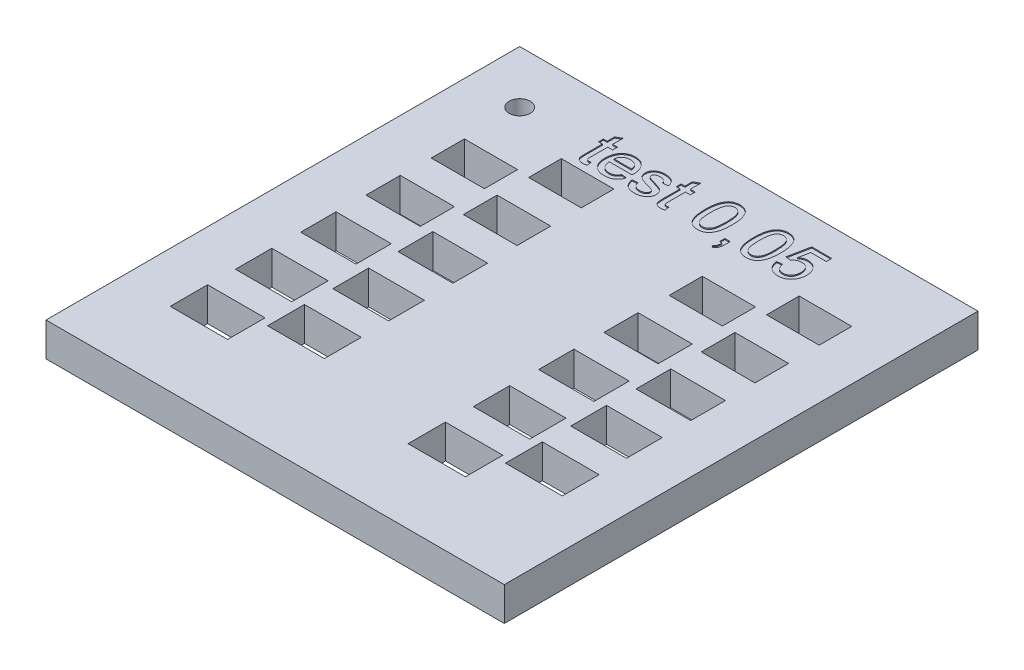
SolidWorks part; units mm, degrees
ref_plane "Спереди" through (0, 0, 0) normal (0, 0, 1) x (1, 0, 0)
ref_plane "Сверху" through (0, 0, 0) normal (0, 1, 0) x (1, 0, 0)
ref_plane "Справа" through (0, 0, 0) normal (1, 0, 0) x (0, 0, -1)
sketch "Эскиз1" plane through (0, 0, 0) normal (0, 1, 0) x (1, 0, 0)
  line L0 (0.0889, -0.0341) -> (43.6285, -0.0341)
  line L1 (43.6285, -0.0341) -> (43.6285, 44.9659)
  line L2 (43.6285, 44.9659) -> (0.0889, 44.9659)
  line L3 (0.0889, 44.9659) -> (0.0889, -0.0341)
  line L5 (11.1389, 16.1656) -> (16.4389, 16.1656)
  line L6 (11.1389, 16.1656) -> (11.1389, 19.5656)
  line L7 (11.1389, 19.5656) -> (16.4389, 19.5656)
  line L8 (16.4389, 16.1656) -> (16.4389, 19.5656)
  line L9 (11.1389, 16.1656) -> (16.4389, 19.5656) construction
  line L10 (11.1389, 19.5656) -> (16.4389, 16.1656) construction
  line L11 (33.7389, 16.1656) -> (39.0389, 16.1656)
  line L12 (33.7389, 16.1656) -> (33.7389, 19.5656)
  line L13 (33.7389, 19.5656) -> (39.0389, 19.5656)
  line L14 (39.0389, 16.1656) -> (39.0389, 19.5656)
  line L15 (33.7389, 16.1656) -> (39.0389, 19.5656) construction
  line L16 (33.7389, 19.5656) -> (39.0389, 16.1656) construction
  line L17 (27.5139, 13.1406) -> (32.8639, 13.1406)
  line L18 (27.5139, 13.1406) -> (27.5139, 16.5906)
  line L19 (27.5139, 16.5906) -> (32.8639, 16.5906)
  line L20 (32.8639, 13.1406) -> (32.8639, 16.5906)
  line L21 (27.5139, 13.1406) -> (32.8639, 16.5906) construction
  line L22 (27.5139, 16.5906) -> (32.8639, 13.1406) construction
  line L23 (33.6889, 10.0156) -> (39.0889, 10.0156)
  line L24 (33.6889, 10.0156) -> (33.6889, 13.5156)
  line L25 (33.6889, 13.5156) -> (39.0889, 13.5156)
  line L26 (39.0889, 10.0156) -> (39.0889, 13.5156)
  line L27 (33.6889, 10.0156) -> (39.0889, 13.5156) construction
  line L28 (33.6889, 13.5156) -> (39.0889, 10.0156) construction
  line L29 (27.4639, 6.9906) -> (32.9139, 6.9906)
  line L30 (27.4639, 6.9906) -> (27.4639, 10.5406)
  line L31 (27.4639, 10.5406) -> (32.9139, 10.5406)
  line L32 (32.9139, 6.9906) -> (32.9139, 10.5406)
  line L33 (27.4639, 6.9906) -> (32.9139, 10.5406) construction
  line L34 (27.4639, 10.5406) -> (32.9139, 6.9906) construction
  line L35 (10.2639, 13.1406) -> (4.9139, 13.1406)
  line L36 (10.2639, 13.1406) -> (10.2639, 16.5906)
  line L37 (11.2389, 28.4656) -> (16.3389, 28.4656)
  line L38 (11.2389, 28.4656) -> (11.2389, 31.6656)
  line L39 (11.2389, 31.6656) -> (16.3389, 31.6656)
  line L40 (16.3389, 28.4656) -> (16.3389, 31.6656)
  line L41 (11.2389, 28.4656) -> (16.3389, 31.6656) construction
  line L42 (11.2389, 31.6656) -> (16.3389, 28.4656) construction
  line L43 (33.8389, 28.4656) -> (38.9389, 28.4656)
  line L44 (5.0139, 25.4406) -> (10.1639, 25.4406)
  line L45 (5.0139, 25.4406) -> (5.0139, 28.6906)
  line L46 (5.0139, 28.6906) -> (10.1639, 28.6906)
  line L47 (10.1639, 25.4406) -> (10.1639, 28.6906)
  line L48 (5.0139, 25.4406) -> (10.1639, 28.6906) construction
  line L49 (5.0139, 28.6906) -> (10.1639, 25.4406) construction
  line L50 (32.7639, 25.4406) -> (27.6139, 25.4406)
  line L51 (32.7639, 25.4406) -> (32.7639, 28.6906)
  line L52 (4.9639, 19.2906) -> (10.2139, 19.2906)
  line L53 (4.9639, 19.2906) -> (4.9639, 22.6406)
  line L54 (4.9639, 22.6406) -> (10.2139, 22.6406)
  line L55 (10.2139, 19.2906) -> (10.2139, 22.6406)
  line L56 (4.9639, 19.2906) -> (10.2139, 22.6406) construction
  line L57 (4.9639, 22.6406) -> (10.2139, 19.2906) construction
  line L58 (32.8139, 19.2906) -> (27.5639, 19.2906)
  line L59 (32.8139, 19.2906) -> (32.8139, 22.6406)
  line L60 (11.1889, 22.3156) -> (16.3889, 22.3156)
  line L61 (11.1889, 22.3156) -> (11.1889, 25.6156)
  line L62 (11.1889, 25.6156) -> (16.3889, 25.6156)
  line L63 (16.3889, 22.3156) -> (16.3889, 25.6156)
  line L64 (11.1889, 22.3156) -> (16.3889, 25.6156) construction
  line L65 (11.1889, 25.6156) -> (16.3889, 22.3156) construction
  line L66 (33.7889, 22.3156) -> (38.9889, 22.3156)
  line L67 (33.7889, 22.3156) -> (33.7889, 25.6156)
  line L68 (33.8389, 28.4656) -> (33.8389, 31.6656)
  line L69 (10.1139, 31.5906) -> (5.0639, 31.5906)
  line L70 (10.1139, 31.5906) -> (10.1139, 34.7406)
  line L71 (10.1139, 34.7406) -> (5.0639, 34.7406)
  line L72 (5.0639, 31.5906) -> (5.0639, 34.7406)
  line L73 (10.1139, 31.5906) -> (5.0639, 34.7406) construction
  line L74 (10.1139, 34.7406) -> (5.0639, 31.5906) construction
  line L75 (32.7139, 31.5906) -> (27.6639, 31.5906)
  line L76 (32.7139, 31.5906) -> (32.7139, 34.7406)
  line L77 (33.8889, 34.6156) -> (38.8889, 34.6156)
  line L78 (33.8889, 34.6156) -> (33.8889, 37.7156)
  line L79 (33.8889, 37.7156) -> (38.8889, 37.7156)
  line L80 (38.8889, 34.6156) -> (38.8889, 37.7156)
  line L81 (11.2889, 34.6156) -> (16.2889, 34.6156)
  line L82 (11.2889, 34.6156) -> (11.2889, 37.7156)
  line L83 (11.2889, 37.7156) -> (16.2889, 37.7156)
  line L84 (7.5889, 49.4234) -> (7.5889, -5.5633) construction
  line L85 (13.7889, 46.9769) -> (13.7889, -3.8081) construction
  line L86 (30.1889, 46.9769) -> (30.1889, -3.457) construction
  line L87 (36.3889, 46.9769) -> (36.3889, -2.8719) construction
  line L88 (-1.9464, 36.1656) -> (47.0659, 36.1656) construction
  line L89 (47.0659, 30.0656) -> (-1.9464, 30.0656) construction
  line L90 (-1.9464, 33.1656) -> (47.0659, 33.1656) construction
  line L91 (-1.9464, 27.0656) -> (47.0659, 27.0656) construction
  line L92 (-1.9464, 23.9656) -> (47.0659, 23.9656) construction
  line L93 (-1.9464, 20.9656) -> (47.0659, 20.9656) construction
  line L94 (-1.9464, 17.8656) -> (47.0659, 17.8656) construction
  line L95 (-1.9464, 14.8656) -> (47.0659, 14.8656) construction
  line L96 (-1.9464, 11.7656) -> (47.0659, 11.7656) construction
  line L97 (-1.9464, 8.7656) -> (47.0659, 8.7656) construction
  line L98 (16.2889, 34.6156) -> (16.2889, 37.7156)
  line L99 (11.2889, 34.6156) -> (16.2889, 37.7156) construction
  line L100 (11.2889, 37.7156) -> (16.2889, 34.6156) construction
  line L101 (33.8889, 34.6156) -> (38.8889, 37.7156) construction
  line L102 (33.8889, 37.7156) -> (38.8889, 34.6156) construction
  line L103 (32.7139, 34.7406) -> (27.6639, 34.7406)
  line L104 (27.6639, 31.5906) -> (27.6639, 34.7406)
  line L105 (32.7139, 31.5906) -> (27.6639, 34.7406) construction
  line L106 (32.7139, 34.7406) -> (27.6639, 31.5906) construction
  line L107 (33.8389, 31.6656) -> (38.9389, 31.6656)
  line L108 (38.9389, 28.4656) -> (38.9389, 31.6656)
  line L109 (33.8389, 28.4656) -> (38.9389, 31.6656) construction
  line L110 (33.8389, 31.6656) -> (38.9389, 28.4656) construction
  line L111 (32.7639, 28.6906) -> (27.6139, 28.6906)
  line L112 (27.6139, 25.4406) -> (27.6139, 28.6906)
  line L113 (32.7639, 25.4406) -> (27.6139, 28.6906) construction
  line L114 (32.7639, 28.6906) -> (27.6139, 25.4406) construction
  line L115 (33.7889, 25.6156) -> (38.9889, 25.6156)
  line L116 (38.9889, 22.3156) -> (38.9889, 25.6156)
  line L117 (33.7889, 22.3156) -> (38.9889, 25.6156) construction
  line L118 (33.7889, 25.6156) -> (38.9889, 22.3156) construction
  line L119 (32.8139, 22.6406) -> (27.5639, 22.6406)
  line L120 (27.5639, 19.2906) -> (27.5639, 22.6406)
  line L121 (32.8139, 19.2906) -> (27.5639, 22.6406) construction
  line L122 (32.8139, 22.6406) -> (27.5639, 19.2906) construction
  line L123 (10.2639, 16.5906) -> (4.9139, 16.5906)
  line L124 (4.9139, 13.1406) -> (4.9139, 16.5906)
  line L125 (10.2639, 13.1406) -> (4.9139, 16.5906) construction
  line L126 (10.2639, 16.5906) -> (4.9139, 13.1406) construction
  line L127 (16.4889, 10.0156) -> (11.0889, 10.0156)
  line L128 (16.4889, 10.0156) -> (16.4889, 13.5156)
  line L129 (16.4889, 13.5156) -> (11.0889, 13.5156)
  line L130 (11.0889, 10.0156) -> (11.0889, 13.5156)
  line L131 (16.4889, 10.0156) -> (11.0889, 13.5156) construction
  line L132 (16.4889, 13.5156) -> (11.0889, 10.0156) construction
  line L133 (4.8639, 6.9906) -> (10.3139, 6.9906)
  line L134 (4.8639, 6.9906) -> (4.8639, 10.5406)
  line L135 (4.8639, 10.5406) -> (10.3139, 10.5406)
  line L136 (10.3139, 6.9906) -> (10.3139, 10.5406)
  line L137 (4.8639, 6.9906) -> (10.3139, 10.5406) construction
  line L138 (4.8639, 10.5406) -> (10.3139, 6.9906) construction
  circle A0 centre (5.0889, 39.9659) radius 1
  point P7 (13.7889, 17.8656)
  point P12 (36.3889, 17.8656)
  point P17 (30.1889, 14.8656)
  point P22 (36.3889, 11.7656)
  point P27 (30.1889, 8.7656)
  point P32 (7.5889, 14.8656)
  point P37 (13.7889, 11.7656)
  point P39 (13.7889, 30.0656)
  point P44 (36.3889, 30.0656)
  point P47 (7.5889, 27.0656)
  point P52 (30.1889, 27.0656)
  point P55 (7.5889, 20.9656)
  point P60 (30.1889, 20.9656)
  point P63 (13.7889, 23.9656)
  point P68 (36.3889, 23.9656)
  point P71 (7.5889, 33.1656)
  point P76 (30.1889, 33.1656)
  point P79 (36.3889, 36.1656)
  point P83 (13.7889, 36.1656)
  point P127 (7.5889, 8.7656)
  dimension "D47" = 2
  dimension "D1" = 43.5396
  dimension "D2" = 45
  dimension "D3" = 7.5
  dimension "D4" = 13.7
  dimension "D5" = 30.1
  dimension "D6" = 36.3
  dimension "D7" = 5
  dimension "D8" = 3.1
  dimension "D9" = 5
  dimension "D10" = 3.1
  dimension "D11" = 5.05
  dimension "D12" = 3.15
  dimension "D13" = 3.15
  dimension "D14" = 5.05
  dimension "D15" = 5.1
  dimension "D16" = 5.1
  dimension "D17" = 3.2
  dimension "D18" = 3.2
  dimension "D19" = 5.15
  dimension "D20" = 5.15
  dimension "D21" = 3.25
  dimension "D22" = 3.25
  dimension "D23" = 5.2
  dimension "D24" = 5.2
  dimension "D25" = 3.3
  dimension "D26" = 3.3
  dimension "D27" = 5.25
  dimension "D28" = 5.25
  dimension "D29" = 3.35
  dimension "D30" = 3.35
  dimension "D31" = 5.3
  dimension "D32" = 5.3
  dimension "D33" = 5.35
  dimension "D34" = 5.35
  dimension "D35" = 5.4
  dimension "D36" = 5.4
  dimension "D37" = 5.45
  dimension "D38" = 5.45
  dimension "D39" = 3.4
  dimension "D40" = 3.4
  dimension "D41" = 3.45
  dimension "D42" = 3.45
  dimension "D43" = 3.5
  dimension "D44" = 3.5
  dimension "D45" = 3.55
  dimension "D46" = 3.55
  dimension "D48" = 5
  dimension "D49" = 5
extrude "Бобышка-Вытянуть1" add sketch "Эскиз1" along normal blind 3.2
sketch "Эскиз2" plane through (0, 3.2, 0) normal (0, 1, 0) x (1, 0, 0)
  text T0 "test 0,05"
extrude "Вырез-Вытянуть1" cut sketch "Эскиз2" against normal blind 0.1
